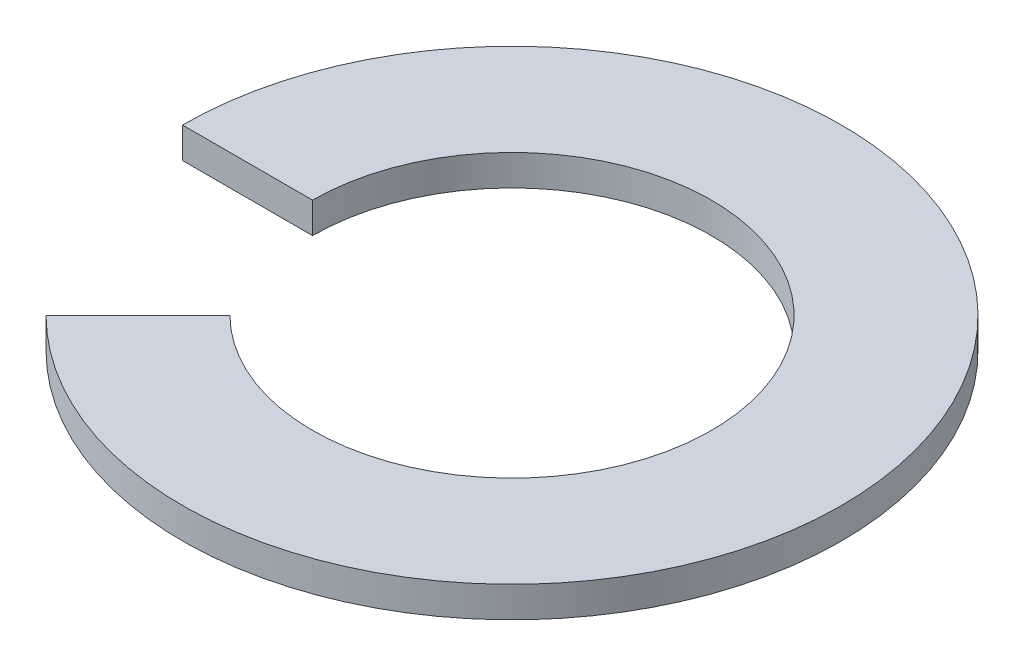
SolidWorks part; units mm, degrees
ref_plane "Front Plane" through (0, 0, 0) normal (0, 0, 1) x (1, 0, 0)
ref_plane "Top Plane" through (0, 0, 0) normal (0, 1, 0) x (1, 0, 0)
ref_plane "Right Plane" through (0, 0, 0) normal (1, 0, 0) x (0, 0, -1)
sketch "Sketch1" plane through (0, 0, 0) normal (0, 1, 0) x (1, 0, 0)
  line L0 (0, 0) -> (-16.0655, 0)
  line L1 (0, 0) -> (-11.36, -11.36)
  arc A0 (-6.8766, -6.8766) -> (-9.725, 0) centre (0, 0) ccw
  arc A1 (-11.36, -11.36) -> (-16.0655, 0) centre (0, 0) ccw
  dimension "D1" = 19.45
  dimension "D2" = 32.131
  dimension "D3" = 45
extrude "Boss-Extrude1" add sketch "Sketch1" along normal blind 1.5 contours L1 A1 L0 A0
